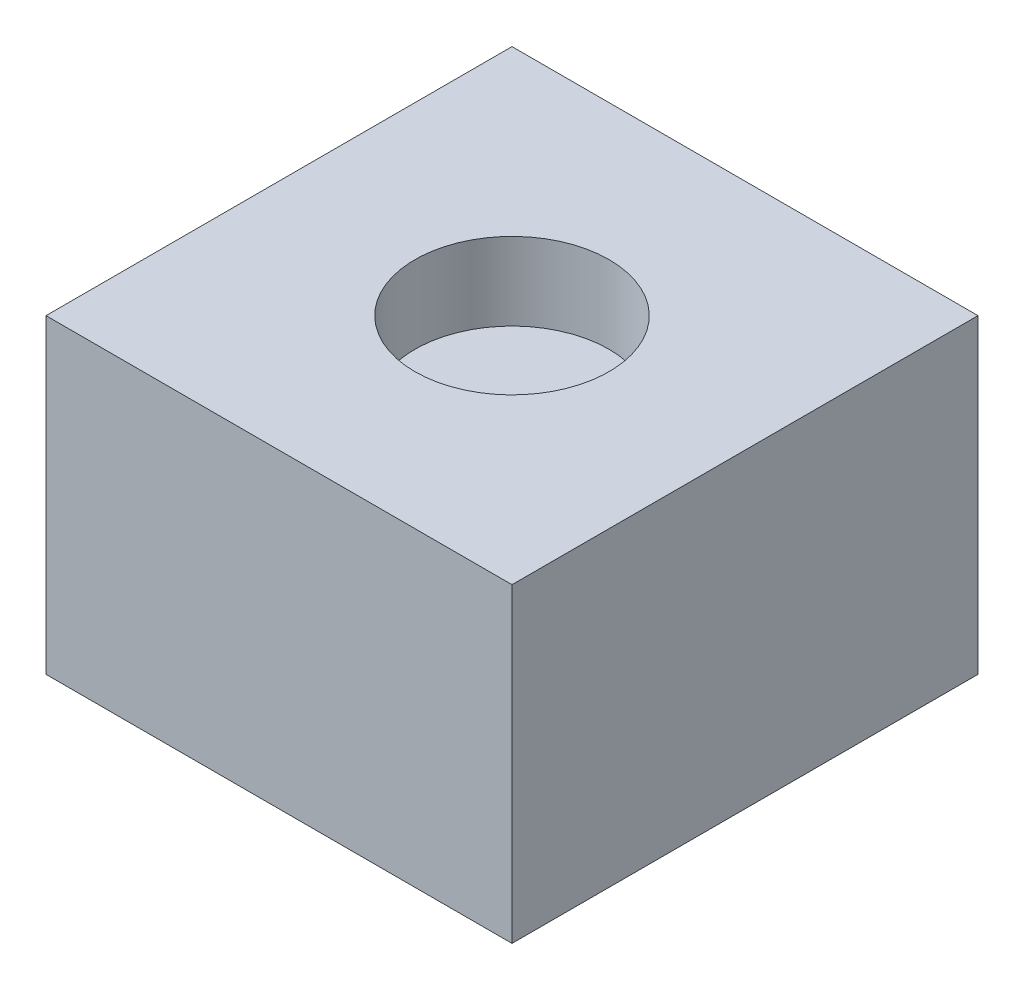
SolidWorks part; units mm, degrees
ref_plane "Front Plane" through (0, 0, 0) normal (0, 0, 1) x (1, 0, 0)
ref_plane "Top Plane" through (0, 0, 0) normal (0, 1, 0) x (1, 0, 0)
ref_plane "Right Plane" through (0, 0, 0) normal (1, 0, 0) x (0, 0, -1)
sketch "Sketch1" plane through (0, 0, 0) normal (0, 1, 0) x (1, 0, 0)
  line L1 (-6, -6) -> (6, -6)
  line L2 (-6, -6) -> (-6, 6)
  line L3 (-6, 6) -> (6, 6)
  line L4 (6, -6) -> (6, 6)
  line L5 (-6, -6) -> (6, 6) construction
  line L6 (-6, 6) -> (6, -6) construction
  point P0 (0, 0)
  dimension "D1" = 12
  dimension "D2" = 12
extrude "Boss-Extrude1" add sketch "Sketch1" along normal blind 8
sketch "Sketch2" plane through (0, 8, 0) normal (0, 1, 0) x (1, 0, 0)
  circle A0 centre (0, 0) radius 2.5
  dimension "D1" = 5
extrude "Cut-Extrude1" cut sketch "Sketch2" against normal blind 2
sketch "Sketch3" plane through (0, 0, 0) normal (0, -1, 0) x (1, 0, 0)
  circle A0 centre (0, 0) radius 1
  dimension "D1" = 2
extrude "Cut-Extrude2" cut sketch "Sketch3" against normal blind 2
fillet "Fillet1" radius 1 1 edges at (0, 2, -1)
